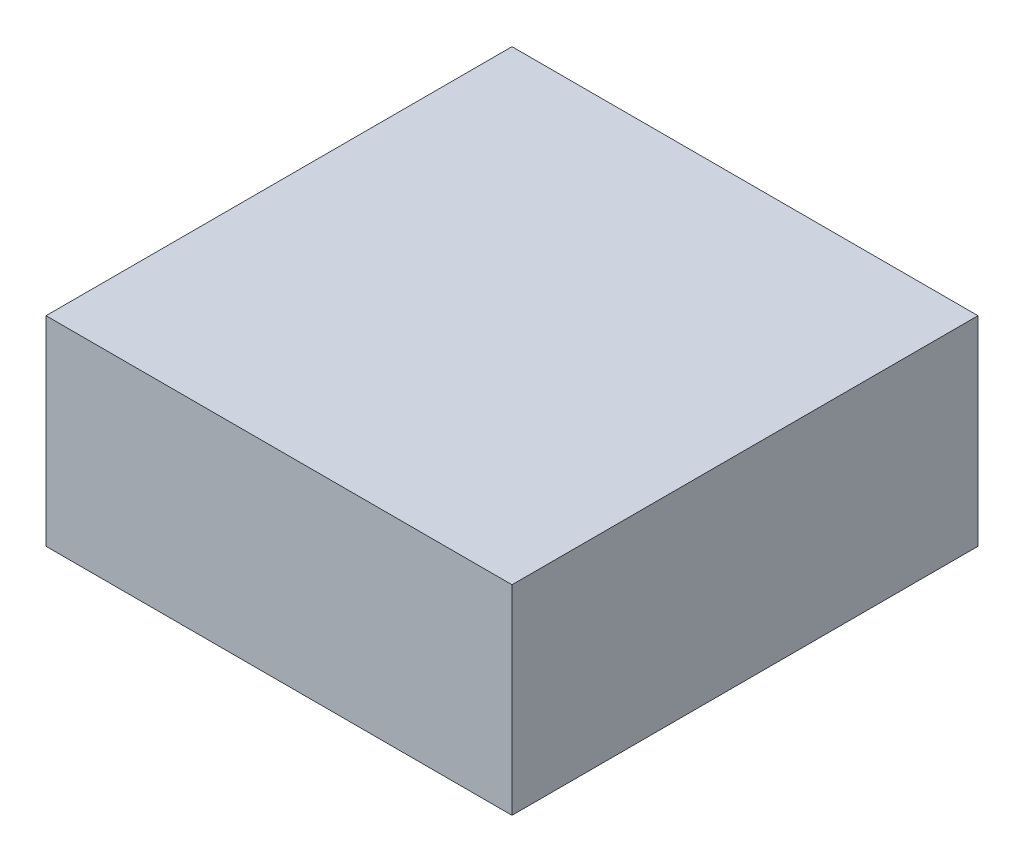
SolidWorks part; units mm, degrees
ref_plane "Front Plane" through (0, 0, 0) normal (0, 0, 1) x (1, 0, 0)
ref_plane "Top Plane" through (0, 0, 0) normal (0, 1, 0) x (1, 0, 0)
ref_plane "Right Plane" through (0, 0, 0) normal (1, 0, 0) x (0, 0, -1)
sketch "Sketch1" plane through (0, 0, 0) normal (0, 1, 0) x (1, 0, 0)
  line L1 (0, 0) -> (88.9, 0)
  line L2 (0, 0) -> (0, -88.9)
  line L3 (0, -88.9) -> (88.9, -88.9)
  line L4 (88.9, 0) -> (88.9, -88.9)
extrude "Boss-Extrude1" add sketch "Sketch1" along normal blind 38.1
sketch "Sketch3" plane through (0, 38.1, 0) normal (0, 1, 0) x (1, 0, 0)
  line L0 (44.45, -88.9) -> (44.45, 0) construction
  line L1 (0, -88.9) -> (88.9, -88.9) construction
  line L2 (88.9, 0) -> (0, 0) construction
  line L3 (88.9, -44.45) -> (0, -44.45) construction
  line L4 (88.9, -88.9) -> (88.9, 0) construction
  line L5 (0, 0) -> (0, -88.9) construction
sketch "Sketch4" plane through (0, 0, 0) normal (0, -1, 0) x (1, 0, 0)
  line L0 (44.45, 0) -> (44.45, 88.9) construction
  line L1 (88.9, 44.45) -> (0, 44.45) construction
